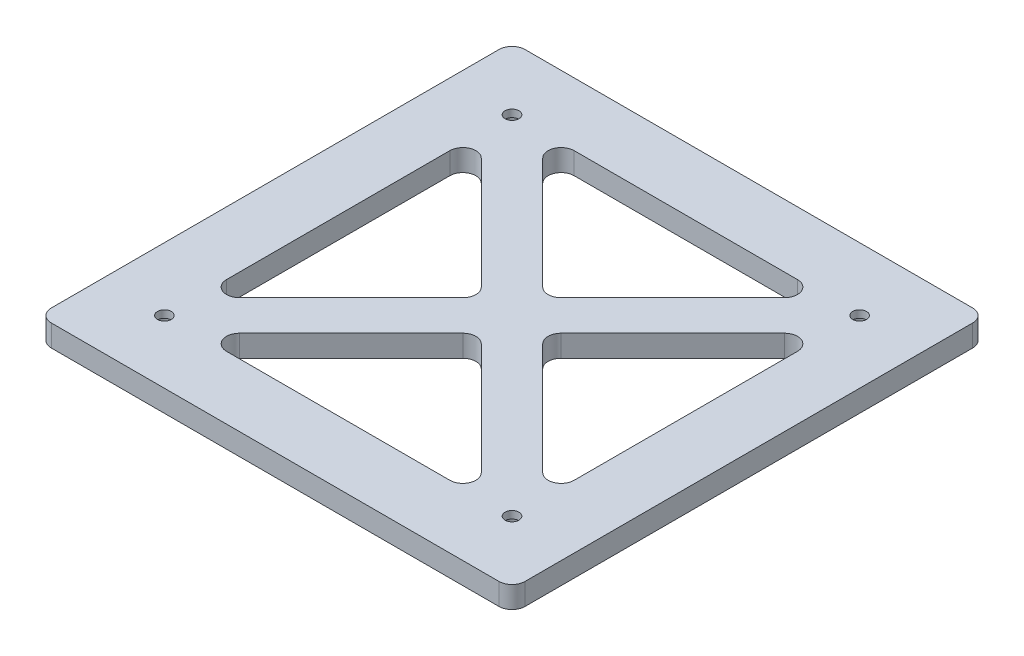
SolidWorks part; units mm, degrees
ref_plane "前视基准面" through (0, 0, 0) normal (0, 0, 1) x (1, 0, 0)
ref_plane "上视基准面" through (0, 0, 0) normal (0, 1, 0) x (1, 0, 0)
ref_plane "右视基准面" through (0, 0, 0) normal (1, 0, 0) x (0, 0, -1)
other "Configuration Table"
sketch "草图1" plane through (0, 0, 0) normal (0, 1, 0) x (1, 0, 0)
  line L0 (14.5, 94.5) -> (94.5, 94.5) construction
  line L1 (0, 0) -> (109, 0)
  line L2 (0, 0) -> (0, 109)
  line L3 (0, 109) -> (109, 109)
  line L4 (109, 0) -> (109, 109)
  line L5 (14.5, 94.5) -> (14.5, 14.5) construction
  line L6 (0, 54.5) -> (109, 54.5) construction
  line L7 (54.5, 109) -> (54.5, 0) construction
  line L8 (14.5, 87.4289) -> (47.4289, 54.5)
  line L9 (47.4289, 54.5) -> (14.5, 21.5711)
  line L10 (14.5, 21.5711) -> (14.5, 87.4289)
  line L11 (21.5711, 94.5) -> (87.4289, 94.5)
  line L12 (87.4289, 94.5) -> (54.5, 61.5711)
  line L13 (54.5, 61.5711) -> (21.5711, 94.5)
  line L14 (94.5, 87.4289) -> (94.5, 21.5711)
  line L15 (94.5, 21.5711) -> (61.5711, 54.5)
  line L16 (61.5711, 54.5) -> (94.5, 87.4289)
  line L17 (87.4289, 14.5) -> (21.5711, 14.5)
  line L18 (21.5711, 14.5) -> (54.5, 47.4289)
  line L19 (54.5, 47.4289) -> (87.4289, 14.5)
  circle A0 centre (14.5, 94.5) radius 1.6
  circle A1 centre (94.5, 94.5) radius 1.6
  circle A2 centre (94.5, 14.5) radius 1.6
  circle A3 centre (14.5, 14.5) radius 1.6
  point P25 (54.5, 54.5)
  point P36 (54.5, 54.5)
  dimension "D8" = 3.2
  dimension "D9" = 40
  dimension "D10" = 40
  dimension "D1" = 109
  dimension "D2" = 109
  dimension "D5" = 90
  dimension "D6" = 80
  dimension "D7" = 80
  dimension "D12" = 10
  dimension "D3" = 2
  dimension "D4" = 2
  dimension "D11" = 4
extrude "凸台-拉伸2" add sketch "草图1" along normal blind 5
fillet "圆角1" radius 3 16 edges at (0, 2.5, 0) (109, 2.5, 0) (109, 2.5, -109) (0, 2.5, -109) (87.4289, 2.5, -14.5) (21.5711, 2.5, -14.5) (54.5, 2.5, -47.4289) (14.5, 2.5, -21.5711) (47.4289, 2.5, -54.5) (94.5, 2.5, -21.5711) (61.5711, 2.5, -54.5) (94.5, 2.5, -87.4289) (54.5, 2.5, -61.5711) (87.4289, 2.5, -94.5) (21.5711, 2.5, -94.5) (14.5, 2.5, -87.4289)
sketch "草图2" plane through (0, 0, 0) normal (0, -1, 0) x (1, 0, 0)
  circle A0 centre (14.5, -14.5) radius 3
  circle A1 centre (94.5, -14.5) radius 3
  circle A2 centre (94.5, -94.5) radius 3
  circle A3 centre (14.5, -94.5) radius 3
  circle A4 centre (14.5, -14.5) radius 1.6 construction
  circle A5 centre (14.5, -94.5) radius 1.6 construction
  circle A6 centre (94.5, -94.5) radius 1.6 construction
  circle A7 centre (94.5, -14.5) radius 1.6 construction
  point P8 (14.5, -14.5)
  dimension "D1" = 6
extrude "切除-拉伸1" cut sketch "草图2" against normal blind 3.3
